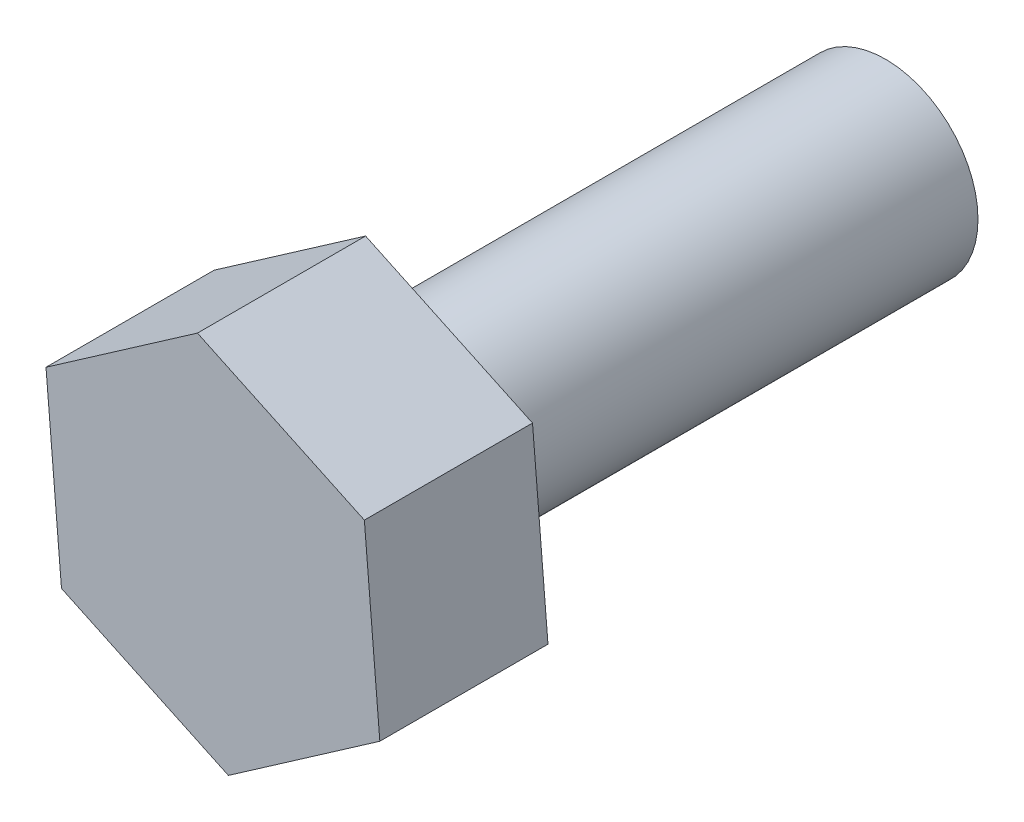
SolidWorks part; units mm, degrees
ref_plane "Front" through (0, 0, 0) normal (0, 0, 1) x (1, 0, 0)
ref_plane "Top" through (0, 0, 0) normal (0, 1, 0) x (1, 0, 0)
ref_plane "Right" through (0, 0, 0) normal (1, 0, 0) x (0, 0, -1)
sketch "Эскиз1" plane through (0, 0, 0) normal (0, 0, 1) x (1, 0, 0)
  circle A0 centre (0, 0) radius 5.5
extrude "Бобышка-Вытянуть1" add sketch "Эскиз1" along normal blind 30 contours A0
sketch "Эскиз2" plane through (0, 0, 30) normal (0, 0, 1) x (1, 0, 0)
  line L1 (-9.9266, 4.6686) -> (-9.0064, -6.2624)
  line L2 (-9.0064, -6.2624) -> (0.9202, -10.931)
  line L3 (0.9202, -10.931) -> (9.9266, -4.6686)
  line L4 (9.9266, -4.6686) -> (9.0064, 6.2624)
  line L5 (9.0064, 6.2624) -> (-0.9202, 10.931)
  line L6 (-0.9202, 10.931) -> (-9.9266, 4.6686)
  circle A0 centre (0, 0) radius 9.5 construction
extrude "Бобышка-Вытянуть2" add sketch "Эскиз2" along normal blind 10
